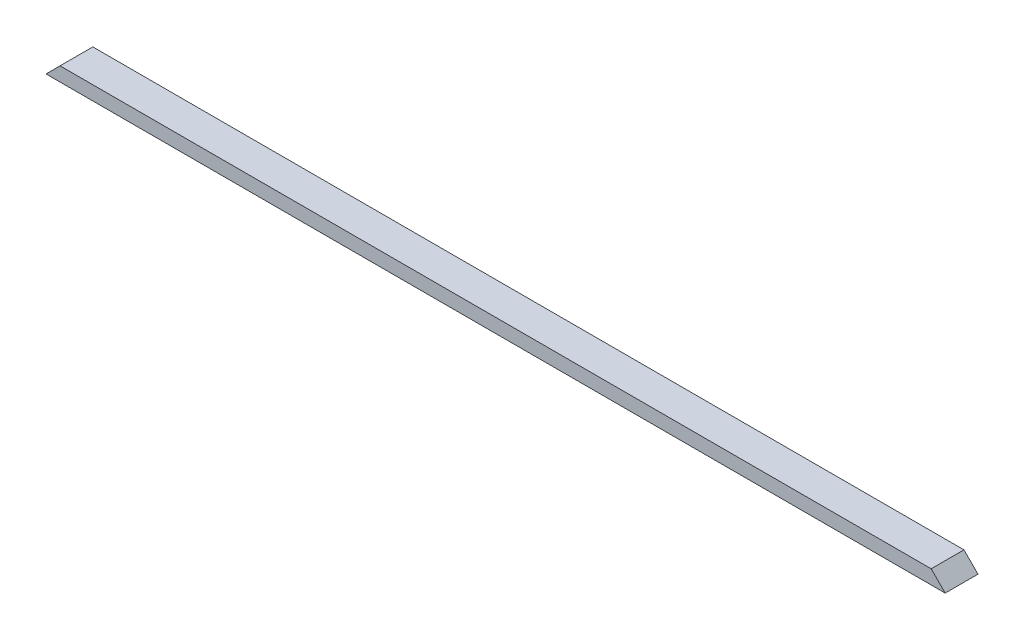
SolidWorks part; units mm, degrees
material "Pine"
ref_plane "Front Plane" through (0, 0, 0) normal (0, 0, 1) x (1, 0, 0)
ref_plane "Top Plane" through (0, 0, 0) normal (0, 1, 0) x (1, 0, 0)
ref_plane "Right Plane" through (0, 0, 0) normal (1, 0, 0) x (0, 0, -1)
sketch "Sketch1" plane through (0, 0, 0) normal (0, 1, 0) x (1, 0, 0)
  line L1 (0, 0) -> (2438.4, 0)
  line L2 (0, 0) -> (0, 88.9)
  line L3 (0, 88.9) -> (2438.4, 88.9)
  line L4 (2438.4, 0) -> (2438.4, 88.9)
  dimension "D1" = 88.9
  dimension "D2" = 2438.4
extrude "Boss-Extrude1" add sketch "Sketch1" along normal blind 38.1
sketch "Sketch2" plane through (0, 0, 0) normal (0, 0, 1) x (1, 0, 0)
  line L0 (0, 0) -> (38.1, 38.1)
  line L1 (0, 38.1) -> (2438.4, 38.1) construction
  line L2 (38.1, 38.1) -> (0, 38.1)
  line L3 (0, 38.1) -> (0, 0)
  line L5 (2438.4, 0) -> (2438.4, 38.1)
  line L9 (2438.4, 38.1) -> (2400.3, 38.1)
  line L10 (2400.3, 38.1) -> (2438.4, 0)
  dimension "D1" = 38.1
  dimension "D2" = 38.1
  dimension "D3" = 38.1
extrude "Cut-Extrude1" cut sketch "Sketch2" against normal through all
